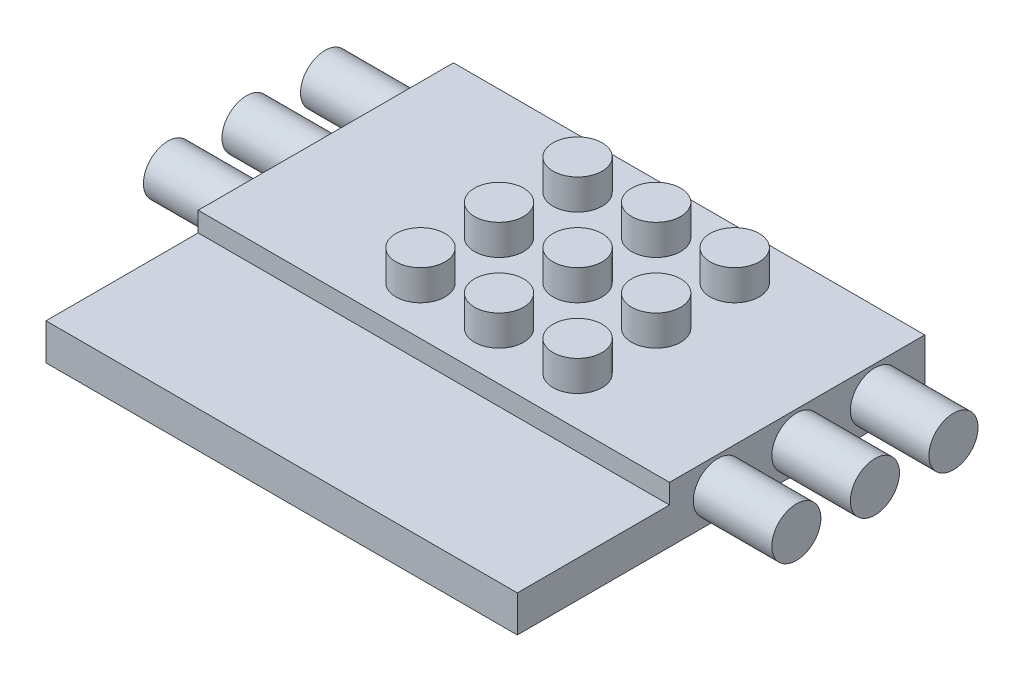
SolidWorks part; units mm, degrees
material "Copper"
ref_plane "Front Plane" through (0, 0, 0) normal (0, 0, 1) x (1, 0, 0)
ref_plane "Top Plane" through (0, 0, 0) normal (0, 1, 0) x (1, 0, 0)
ref_plane "Right Plane" through (0, 0, 0) normal (1, 0, 0) x (0, 0, -1)
ref_plane "Plane2" through (0, 1.5875, 0) normal (0, 1, 0) x (-1, 0, 0)
sketch "Sketch3" plane through (0, 1.5875, 0) normal (0, 1, 0) x (-1, 0, 0)
  line L1 (-10.75, -16) -> (-17.5, -16)
  line L2 (-10.75, -16) -> (-10.75, -26.25)
  line L3 (-10.75, -26.25) -> (-17.5, -26.25)
  line L4 (-17.5, -16) -> (-17.5, -26.25)
extrude "Boss-Extrude2" add sketch "Sketch3" along normal blind 4.4125
ref_plane "Plane3" through (0, 3.1375, 0) normal (0, -1, 0) x (-1, 0, 0)
sketch "Sketch5" plane through (0, 3.1375, 0) normal (0, -1, 0) x (1, 0, 0)
  circle A0 centre (16.36, -24.96) radius 1.25
  circle A1 centre (12.36, -24.96) radius 1.25
  circle A2 centre (8.36, -24.96) radius 1.25
  circle A3 centre (16.36, -20.96) radius 1.25
  circle A4 centre (12.36, -20.96) radius 1.25
  circle A5 centre (8.36, -20.96) radius 1.25
  circle A6 centre (16.36, -16.96) radius 1.25
  circle A7 centre (12.36, -16.96) radius 1.25
  circle A8 centre (8.36, -16.96) radius 1.25
  dimension "D1" = 3
  dimension "D2" = 3
extrude "Boss-Extrude3" add sketch "Sketch5" along normal blind 3.1375 and the other way blind 4.4125
sketch "Sketch6" plane through (17.5, 0, 0) normal (1, 0, 0) x (0, 0, -1)
  line L0 (16, 6) -> (16.4473, 6) construction
  line L1 (6.75, 6) -> (27.5, 6)
  line L2 (6.75, 6) -> (6.75, 3.1425)
  line L3 (6.75, 3.1425) -> (27.5, 3.1425)
  line L4 (27.5, 6) -> (27.5, 3.1425)
extrude "Boss-Extrude4" add sketch "Sketch6" along normal blind 6 and the other way blind 18
sketch "Sketch11" plane through (0, 3.1425, 0) normal (0, -1, 0) x (1, 0, 0)
  line L1 (5.3068, -27.8263) -> (10.2105, -27.8263)
  line L2 (5.3068, -27.8263) -> (5.3068, -14.0312)
  line L3 (5.3068, -14.0312) -> (10.2105, -14.0312)
  line L4 (10.2105, -27.8263) -> (10.2105, -14.0312)
extrude "Cut-Extrude1" cut sketch "Sketch11" along normal blind 4.1425
sketch "Sketch12" plane through (0, 6, 0) normal (0, 1, 0) x (1, 0, 0)
  line L1 (-0.9882, 14.5) -> (23.8217, 14.5)
  line L2 (-0.9882, 14.5) -> (-0.9882, 5.7304)
  line L3 (-0.9882, 5.7304) -> (23.8217, 5.7304)
  line L4 (23.8217, 14.5) -> (23.8217, 5.7304)
extrude "Cut-Extrude2" cut sketch "Sketch12" against normal blind 1
sketch "Sketch13" plane through (23.5, 0, 0) normal (1, 0, 0) x (0, 0, -1)
  line L0 (27.5, 4.5713) -> (6.75, 4.5713) construction
  line L1 (27.5, 3.1425) -> (27.5, 6) construction
  line L2 (6.75, 5) -> (6.75, 3.1425) construction
  circle A0 centre (24.96, 4.5713) radius 1.25
  circle A1 centre (16.96, 4.5713) radius 1.25
  circle A2 centre (20.96, 4.5712) radius 1.25
extrude "Boss-Extrude8" add sketch "Sketch13" along normal blind 4 and the other way blind 28
sketch "Sketch14" plane through (0, 0, -16) normal (0, 0, 1) x (1, 0, 0)
  line L1 (10.75, 3.1425) -> (18.1627, 3.1425)
  line L2 (10.75, 3.1425) -> (10.75, -1.118)
  line L3 (10.75, -1.118) -> (18.1627, -1.118)
  line L4 (18.1627, 3.1425) -> (18.1627, -1.118)
extrude "Cut-Extrude3" cut sketch "Sketch14" along normal up to next (1.5 mm away)
sketch "Sketch15" plane through (17.5, 0, 0) normal (1, 0, 0) x (0, 0, -1)
  line L1 (16, 3.1425) -> (26.9231, 3.1425)
  line L2 (16, 3.1425) -> (16, -1.0209)
  line L3 (16, -1.0209) -> (26.9231, -1.0209)
  line L4 (26.9231, 3.1425) -> (26.9231, -1.0209)
extrude "Cut-Extrude4" cut sketch "Sketch15" along normal up to next
